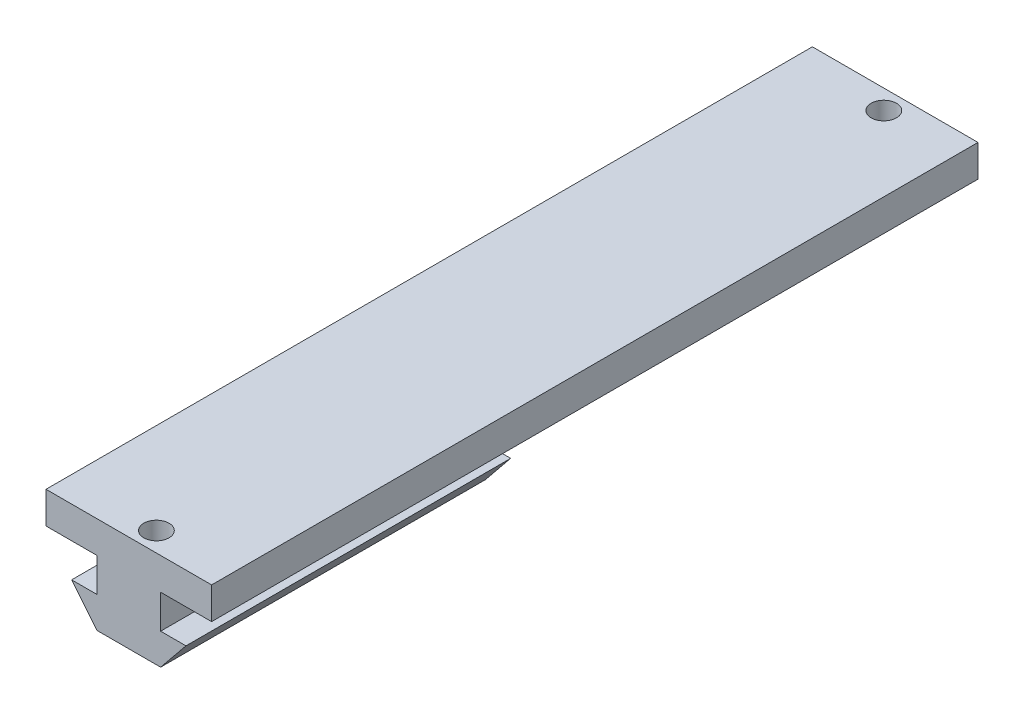
SolidWorks part; units mm, degrees
ref_plane "Front Plane" through (0, 0, 0) normal (0, 0, 1) x (1, 0, 0)
ref_plane "Top Plane" through (0, 0, 0) normal (0, 1, 0) x (1, 0, 0)
ref_plane "Right Plane" through (0, 0, 0) normal (1, 0, 0) x (0, 0, -1)
sketch "Sketch1" plane through (0, 0, 0) normal (0, 1, 0) x (1, 0, 0)
  line L1 (-12.75, -59) -> (12.75, -59)
  line L2 (-12.75, -59) -> (-12.75, 59)
  line L3 (-12.75, 59) -> (12.75, 59)
  line L4 (12.75, -59) -> (12.75, 59)
  line L5 (-12.75, -59) -> (12.75, 59) construction
  line L6 (-12.75, 59) -> (12.75, -59) construction
  point P0 (0, 0)
  dimension "D1" = 118
  dimension "D2" = 25.5
extrude "Boss-Extrude1" add sketch "Sketch1" along normal blind 4.9
sketch "Sketch2" plane through (0, 4.9, 0) normal (0, 1, 0) x (1, 0, 0)
  line L0 (12.75, 0) -> (-12.75, 0) construction
  line L1 (12.75, -59) -> (12.75, 59) construction
  line L2 (-12.75, 59) -> (-12.75, -59) construction
  circle A0 centre (1.25, 56) radius 1.95
  circle A1 centre (1.25, -56) radius 1.95
  dimension "D1" = 3.9
  dimension "D2" = 112
  dimension "D3" = 14
sketch "Sketch5" plane through (0, 0, 59) normal (0, 0, 1) x (1, 0, 0)
  line L1 (-12.75, 0) -> (12.75, 0) construction
  line L2 (-4.9, 0) -> (-4.9, -5.2)
  line L4 (-4.9, -10) -> (4.9, -10)
  line L6 (4.9, -5.2) -> (4.9, 0)
  line L7 (4.9, 0) -> (-4.9, 0)
  line L8 (0, 0) -> (0, -10) construction
  line L9 (-4.9, -5.2) -> (-8.8, -5.2)
  line L10 (-8.8, -5.2) -> (-4.9, -10)
  line L11 (4.9, -5.2) -> (8.8, -5.2)
  line L12 (8.8, -5.2) -> (4.9, -10)
  dimension "D1" = 5.2
  dimension "D2" = 4.8
  dimension "D3" = 3.9
  dimension "D4" = 9.8
extrude "Boss-Extrude5" add sketch "Sketch5" along direction (0, 0, -1) on the side against the normal blind 50
extrude "Cut-Extrude1" cut sketch "Sketch2" against normal blind 10
